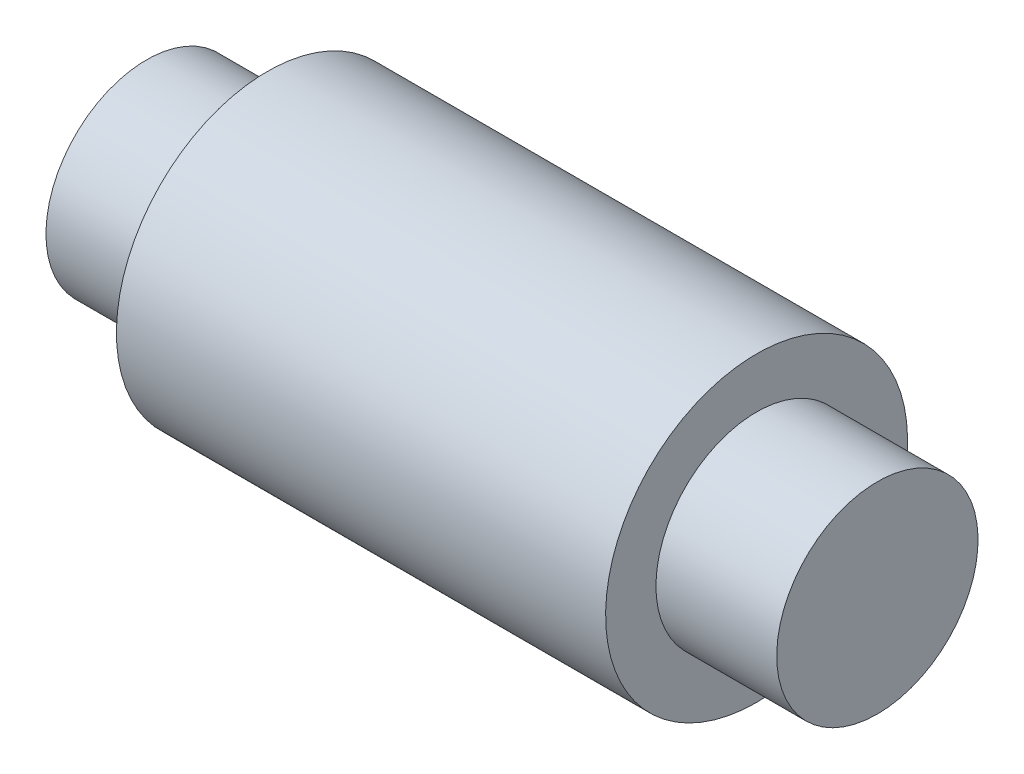
SolidWorks part; units mm, degrees
material "1060 Alloy"
ref_plane "Front Plane" through (0, 0, 0) normal (0, 0, 1) x (1, 0, 0)
ref_plane "Top Plane" through (0, 0, 0) normal (0, 1, 0) x (1, 0, 0)
ref_plane "Right Plane" through (0, 0, 0) normal (1, 0, 0) x (0, 0, -1)
sketch "Sketch1" plane through (0, 0, 0) normal (0, 0, 1) x (1, 0, 0)
  line L0 (0, 0) -> (0, -10)
  line L1 (0, -10) -> (72.6, -10)
  line L2 (72.6, -10) -> (72.6, 0)
  line L3 (72.6, 0) -> (60.6, 0)
  line L4 (60.6, 0) -> (60.6, 5)
  line L5 (60.6, 5) -> (12, 5)
  line L6 (12, 5) -> (12, 0)
  line L7 (12, 0) -> (0, 0)
  dimension "D1" = 10
  dimension "D2" = 5
  dimension "D3" = 12
  dimension "D4" = 12
  dimension "D5" = 48.6
revolve "Revolve1" add sketch "Sketch1" angle 360 about L1
